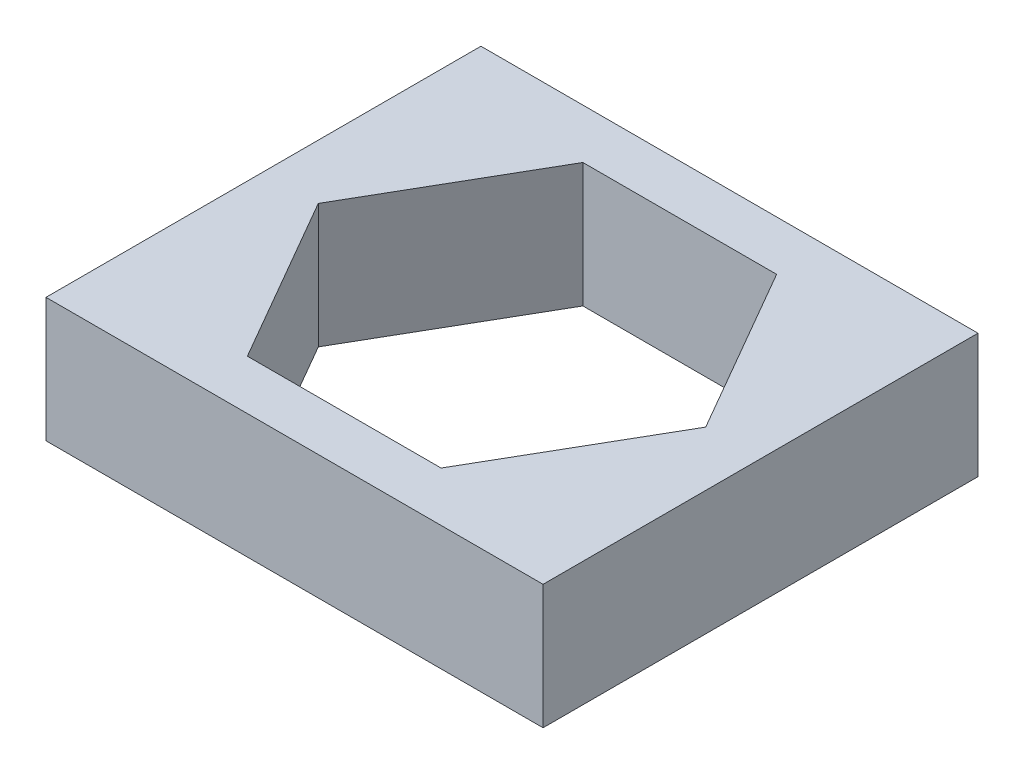
SolidWorks part; units mm, degrees
ref_plane "Front Plane" through (0, 0, 0) normal (0, 0, 1) x (1, 0, 0)
ref_plane "Top Plane" through (0, 0, 0) normal (0, 1, 0) x (1, 0, 0)
ref_plane "Right Plane" through (0, 0, 0) normal (1, 0, 0) x (0, 0, -1)
sketch "Sketch1" plane through (0, 0, 0) normal (0, 1, 0) x (1, 0, 0)
  line L1 (0, 0) -> (8, 0)
  line L2 (0, 0) -> (0, 7)
  line L3 (0, 7) -> (8, 7)
  line L4 (8, 0) -> (8, 7)
  line L5 (7.1177, 3.5) -> (5.5588, 6.2)
  line L6 (5.5588, 6.2) -> (2.4412, 6.2)
  line L7 (2.4412, 6.2) -> (0.8823, 3.5)
  line L8 (0.8823, 3.5) -> (2.4412, 0.8)
  line L9 (2.4412, 0.8) -> (5.5588, 0.8)
  line L10 (5.5588, 0.8) -> (7.1177, 3.5)
  circle A0 centre (4, 3.5) radius 2.7 construction
  point P6 (0, 0)
  point P14 (4, 0)
  point P15 (0, 0)
  point P16 (0, 3.5)
  dimension "D1" = 5.4
  dimension "D2" = 8
  dimension "D3" = 7
extrude "Boss-Extrude1" add sketch "Sketch1" along normal blind 2
